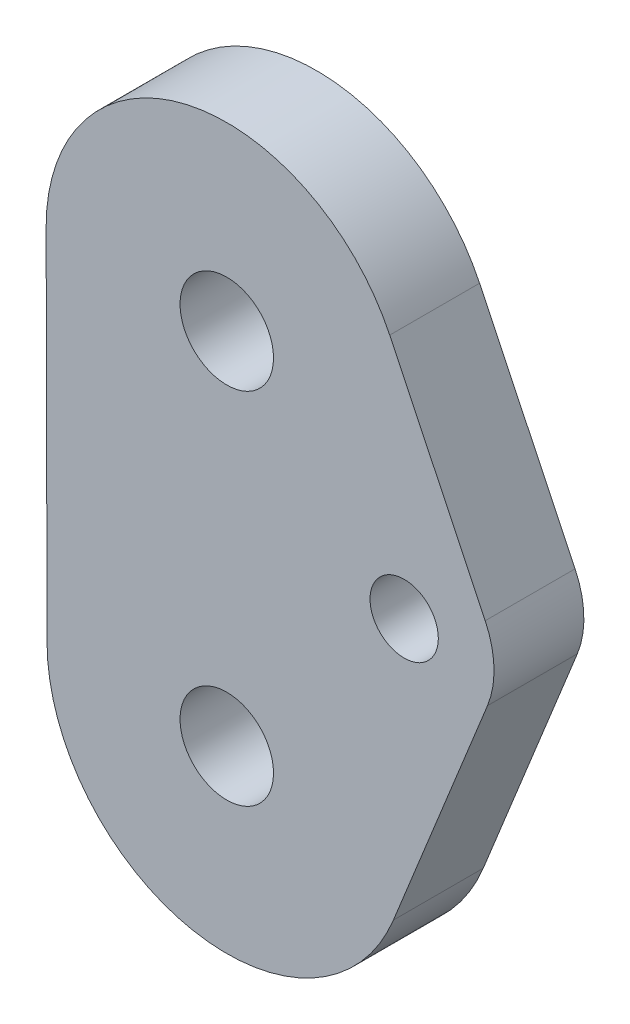
SolidWorks part; units mm, degrees
material "6061-T6 (SS)"
ref_plane "Front Plane" through (0, 0, 0) normal (0, 0, 1) x (1, 0, 0)
ref_plane "Top Plane" through (0, 0, 0) normal (0, 1, 0) x (1, 0, 0)
ref_plane "Right Plane" through (0, 0, 0) normal (1, 0, 0) x (0, 0, -1)
sketch "Sketch1" plane through (0, 0, 0) normal (0, 0, 1) x (1, 0, 0)
  line L3 (62.8729, -55.8232) -> (56.2242, -72.2689)
  line L4 (31.75, -67.5413) -> (31.685, -42.1414)
  line L5 (55.9645, -36.5985) -> (62.7138, -50.702)
  circle A6 centre (56.9859, -53.4431) radius 2.413
  arc A7 (62.8729, -55.8232) -> (62.7138, -50.702) centre (56.9859, -53.4431) ccw
  arc A8 (31.75, -67.5413) -> (56.2242, -72.2689) centre (44.45, -67.5087) ccw
  circle A9 centre (44.45, -67.5087) radius 3.302
  circle A10 centre (44.45, -42.1087) radius 3.302
  arc A11 (55.9645, -36.5985) -> (31.685, -42.1414) centre (44.45, -42.1087) ccw
extrude "Boss-Extrude1" add sketch "Sketch1" along normal blind 6.35
equation "\"Thick\"= \"in\""
